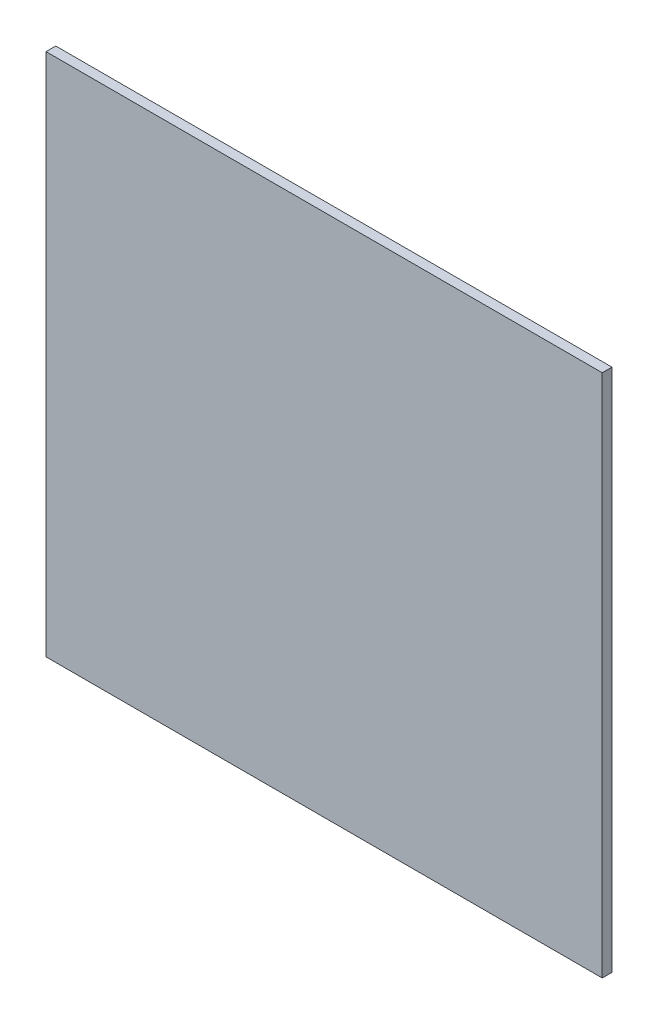
SolidWorks part; units mm, degrees
ref_plane "Front Plane" through (0, 0, 0) normal (0, 0, 1) x (1, 0, 0)
ref_plane "Top Plane" through (0, 0, 0) normal (0, 1, 0) x (1, 0, 0)
ref_plane "Right Plane" through (0, 0, 0) normal (1, 0, 0) x (0, 0, -1)
sketch "Sketch1" plane through (0, 0, 0) normal (0, 0, 1) x (1, 0, 0)
  line L1 (-114.6516, -524.6255) -> (56.6303, -524.6255)
  line L2 (-114.6516, -524.6255) -> (-114.6516, -363.214)
  line L3 (-114.6516, -363.214) -> (56.6303, -363.214)
  line L4 (56.6303, -524.6255) -> (56.6303, -363.214)
extrude "Boss-Extrude1" add sketch "Sketch1" along normal blind 3
